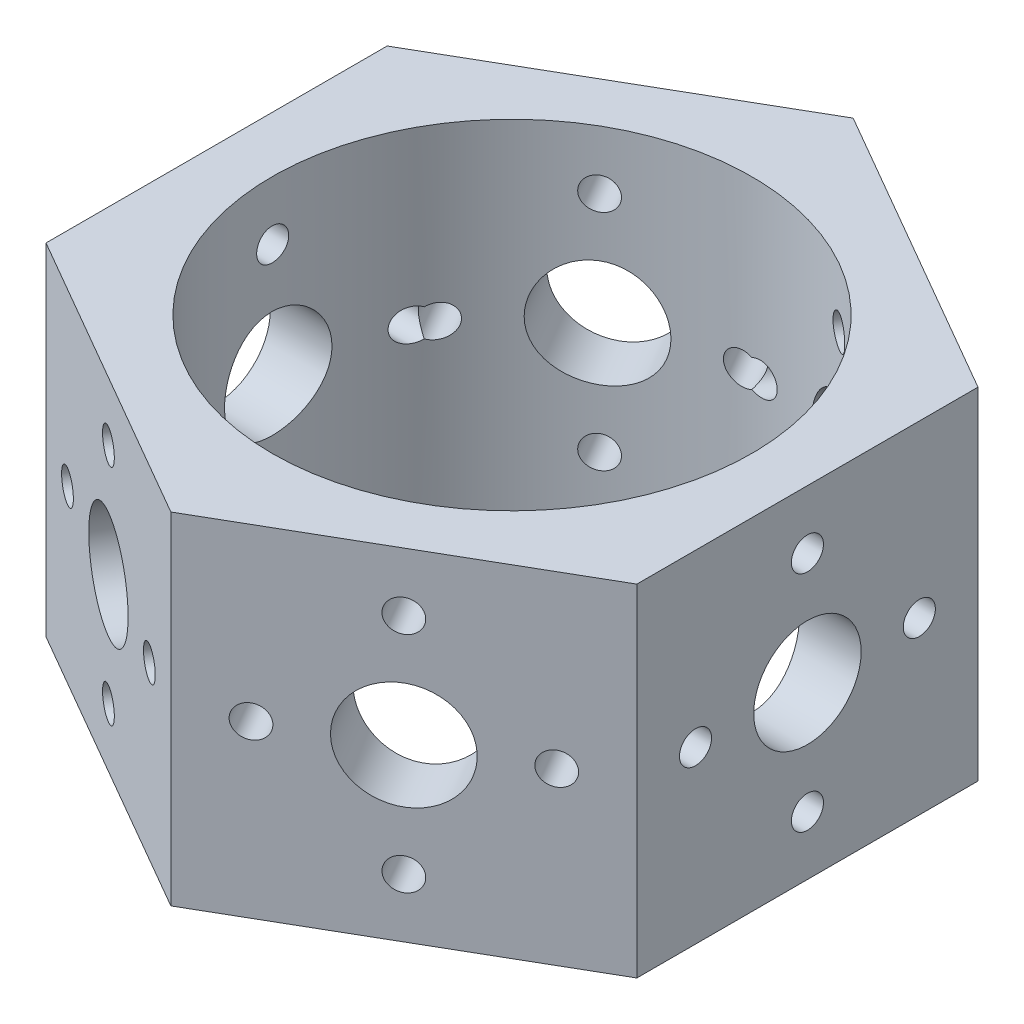
SolidWorks part; units mm, degrees
ref_plane "Front" through (0, 0, 0) normal (0, 0, 1) x (1, 0, 0)
ref_plane "Top" through (0, 0, 0) normal (0, 1, 0) x (1, 0, 0)
ref_plane "Right" through (0, 0, 0) normal (1, 0, 0) x (0, 0, -1)
sketch "Sketch1" plane through (0, 0, 0) normal (0, 1, 0) x (1, 0, 0)
  line L4 (-21.9964, 12.7) -> (-21.9967, -12.6994)
  line L5 (-21.9967, -12.6994) -> (-0.0003, -25.3994)
  line L6 (-0.0003, -25.3994) -> (21.9964, -12.7)
  line L7 (21.9964, -12.7) -> (21.9967, 12.6994)
  line L8 (21.9967, 12.6994) -> (0.0003, 25.3994)
  line L9 (0.0003, 25.3994) -> (-21.9964, 12.7)
  circle A0 centre (0, 0) radius 17.8562
  circle A1 centre (0, 0) radius 21.9966 construction
extrude "Extrude1" add sketch "Sketch1" along normal blind 25.4
sketch "Sketch2" plane through (0, 0, 0) normal (1, 0, 0) x (0, 0, -1)
  circle A0 centre (-0.0003, 12.7) radius 4.0005
  circle A2 centre (8.3309, 12.7) radius 1.1938
  circle A3 centre (-0.0003, 4.3688) radius 1.1938
  circle A4 centre (-8.3315, 12.7) radius 1.1938
  circle A5 centre (-0.0003, 21.0312) radius 1.1938
extrude "Cut-Extrude1" cut sketch "Sketch2" against normal blind 25.4 and the other way blind 25.4
ref_plane "Plane1" through (0, 0, 0) normal (-0.5, 0, 0.866) x (0.866, 0, 0.5)
sketch "Sketch3" plane through (0, 0, 0) normal (-0.5, 0, 0.866) x (0.866, 0, 0.5)
  circle A0 centre (0, 12.7) radius 4.0005
  circle A1 centre (8.3312, 12.7) radius 1.1938
  circle A2 centre (0, 4.3688) radius 1.1938
  circle A3 centre (-8.3312, 12.7) radius 1.1938
  circle A4 centre (0, 21.0312) radius 1.1938
extrude "Cut-Extrude2" cut sketch "Sketch3" against normal blind 25.4 and the other way blind 25.4
ref_plane "Plane2" through (0, 0, 0) normal (-0.5, 0, -0.866) x (-0.866, 0, 0.5)
sketch "Sketch4" plane through (0, 0, 0) normal (-0.5, 0, -0.866) x (-0.866, 0, 0.5)
  circle A0 centre (0, 12.7) radius 4.0005
  circle A1 centre (8.3312, 12.7) radius 1.1938
  circle A2 centre (0, 4.3688) radius 1.1938
  circle A3 centre (-8.3312, 12.7) radius 1.1938
  circle A4 centre (0, 21.0312) radius 1.1938
extrude "Cut-Extrude3" cut sketch "Sketch4" against normal blind 25.4 and the other way blind 25.4
